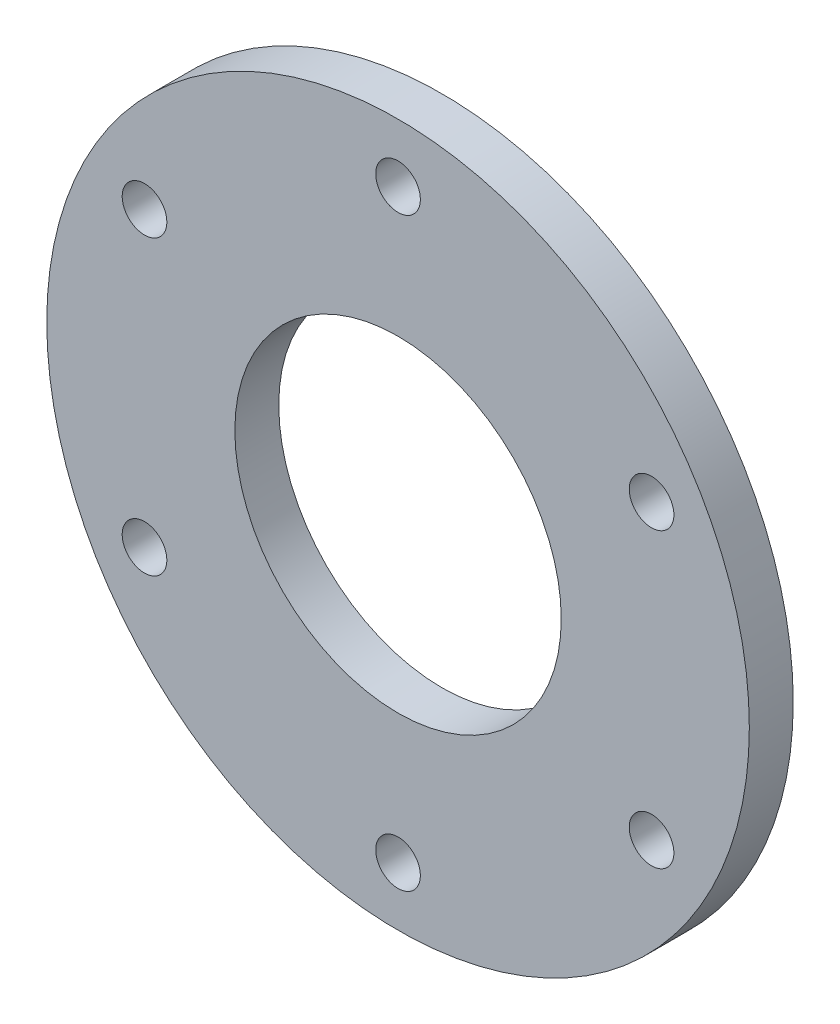
SolidWorks part; units mm, degrees
material "Thornel Mat VMA"
ref_plane "前视基准面" through (0, 0, 0) normal (0, 0, 1) x (1, 0, 0)
ref_plane "上视基准面" through (0, 0, 0) normal (0, 1, 0) x (1, 0, 0)
ref_plane "右视基准面" through (0, 0, 0) normal (1, 0, 0) x (0, 0, -1)
sketch "草图1" plane through (0, 0, 0) normal (0, 0, 1) x (1, 0, 0)
  circle A0 centre (0, 0) radius 11.15
  circle A1 centre (0, 0) radius 12.5 construction
  circle A2 centre (0, 0) radius 20 construction
  circle A3 centre (0, 0) radius 24
  circle A4 centre (0, 20) radius 1.525
  circle A5 centre (17.3205, 10) radius 1.525
  circle A6 centre (17.3205, -10) radius 1.525
  circle A7 centre (0, -20) radius 1.525
  circle A8 centre (-17.3205, -10) radius 1.525
  circle A9 centre (-17.3205, 10) radius 1.525
  circle A10 centre (0, 12.5) radius 1.4 construction
  circle A11 centre (10.8253, -6.25) radius 1.4 construction
  circle A12 centre (-10.8253, -6.25) radius 1.4 construction
  point P20 (0, 0)
  point P27 (0, 0)
  dimension "D1" = 22.3
  dimension "D2" = 25
  dimension "D3" = 40
  dimension "D4" = 48
  dimension "D5" = 3.05
  dimension "D7" = 2.8
  dimension "D6" = 6
  dimension "D8" = 3
extrude "凸台-拉伸1" add sketch "草图1" along normal blind 3
